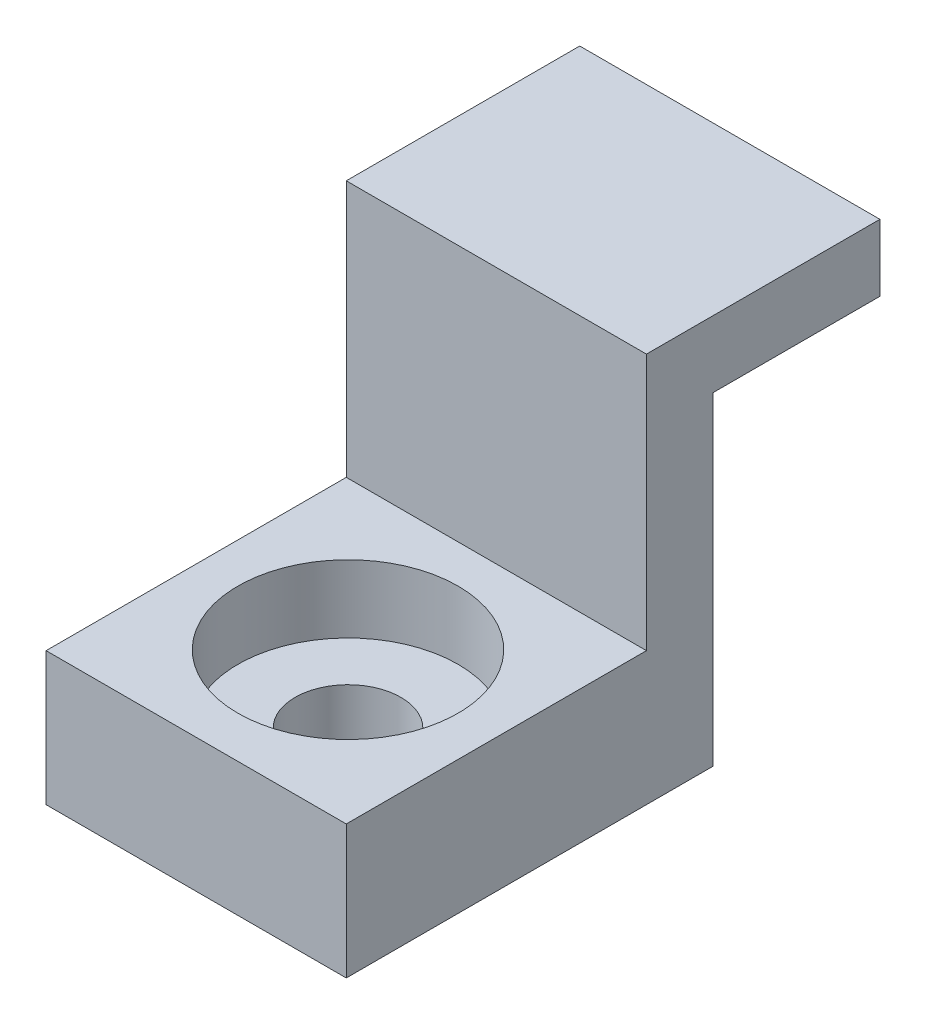
SolidWorks part; units mm, degrees
ref_plane "Front Plane" through (0, 0, 0) normal (0, 0, 1) x (1, 0, 0)
ref_plane "Top Plane" through (0, 0, 0) normal (0, 1, 0) x (1, 0, 0)
ref_plane "Right Plane" through (0, 0, 0) normal (1, 0, 0) x (0, 0, -1)
sketch "Sketch1" plane through (0, 0, 0) normal (0, 0, 1) x (1, 0, 0)
  line L1 (-92.4301, -5.25) -> (-83.4301, -5.25)
  line L2 (-92.4301, -5.25) -> (-92.4301, 6.45)
  line L3 (-92.4301, 6.45) -> (-83.4301, 6.45)
  line L4 (-83.4301, -5.25) -> (-83.4301, 6.45)
  dimension "D1" = 9
  dimension "D2" = 11.7
  dimension "D3" = 83.4301
extrude "Boss-Extrude1" add sketch "Sketch1" along normal blind 2 separate body
sketch "Sketch2" plane through (0, 0, 0) normal (0, 0, -1) x (-1, 0, 0)
  line L0 (92.4301, 6.45) -> (92.4301, -5.25) construction
  line L1 (83.4301, 6.45) -> (92.4301, 6.45)
  line L2 (83.4301, 6.45) -> (83.4301, 4.45)
  line L3 (83.4301, 4.45) -> (92.4301, 4.45)
  line L4 (92.4301, 6.45) -> (92.4301, 4.45)
  dimension "D1" = 2
extrude "Boss-Extrude2" add sketch "Sketch2" along normal blind 5
sketch "Sketch3" plane through (0, 0, 2) normal (0, 0, 1) x (1, 0, 0)
  line L0 (-83.4301, -5.25) -> (-83.4301, 6.45) construction
  line L1 (-92.4301, -5.25) -> (-83.4301, -5.25)
  line L2 (-92.4301, -5.25) -> (-92.4301, -1.25)
  line L3 (-92.4301, -1.25) -> (-83.4301, -1.25)
  line L4 (-83.4301, -5.25) -> (-83.4301, -1.25)
  dimension "D1" = 4
extrude "Boss-Extrude3" add sketch "Sketch3" along normal blind 9
hole_wizard "CBORE for #4 Binding Head Machine Screw1" positions "Sketch4" profile "Sketch5" counterbore size "#4" standard "ANSI Inch" end condition through all
sketch "Sketch4" plane through (0, -1.25, 0) normal (0, 1, 0) x (1, 0, 0)
  point P0 (-87.9301, -6.4482)
  point P8 (-88.6915, -7.3839)
  point P9 (-87.9301, -6.4482)
sketch "Sketch5" plane through (-87.9301, -1.25, 6.4482) normal (1, 0, 0) x (0, 0, 1)
  line L0 (0, 0) -> (0, 4)
  line L1 (0, 4) -> (1.5875, 4)
  line L3 (1.5875, 4) -> (1.5875, 2.032)
  line L4 (1.5875, 2.032) -> (3.302, 2.032)
  line L5 (3.302, 2.032) -> (3.302, 0)
  line L7 (3.302, 0) -> (0, 0)
  line L11 (0, -6.35) -> (0, 107.95) construction
  dimension "Thru Hole Dia." = 3.175
  dimension "Thru Hole Depth" = 4
  dimension "C'Bore Dia." = 6.604
  dimension "C'Bore Depth" = 2.032
